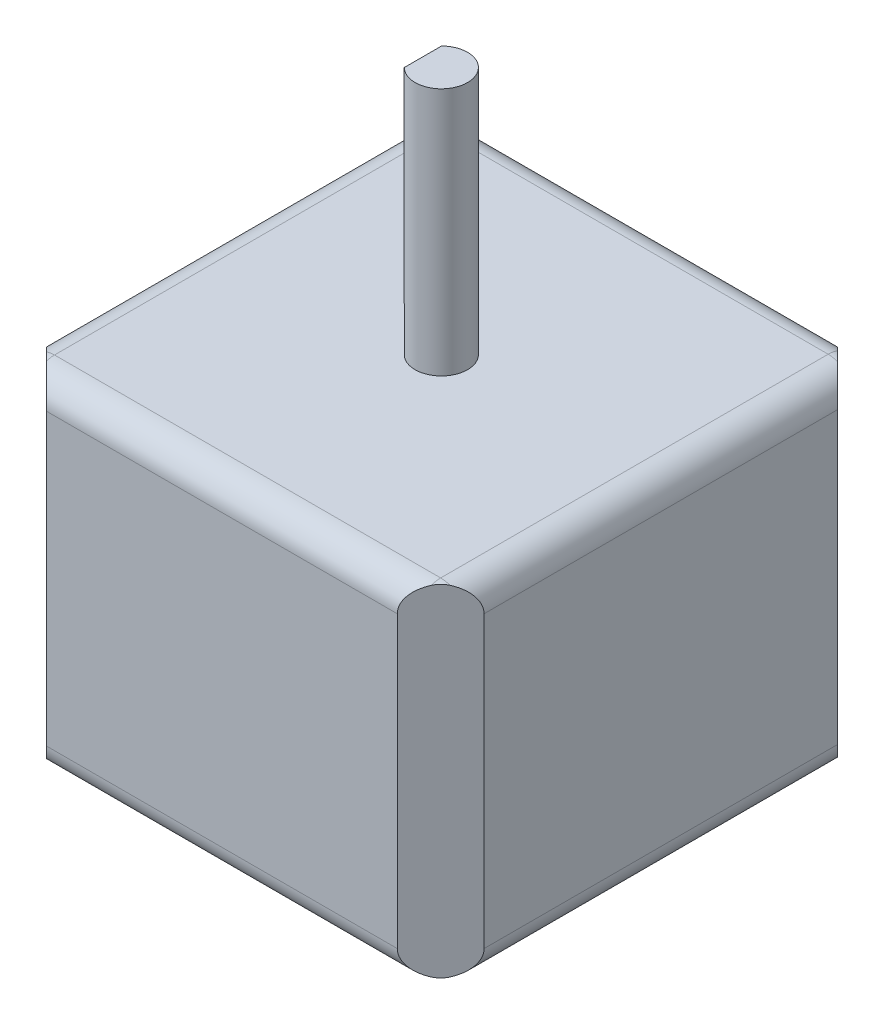
SolidWorks part; units mm, degrees
ref_plane "Front Plane" through (0, 0, 0) normal (0, 0, 1) x (1, 0, 0)
ref_plane "Top Plane" through (0, 0, 0) normal (0, 1, 0) x (1, 0, 0)
ref_plane "Right Plane" through (0, 0, 0) normal (1, 0, 0) x (0, 0, -1)
sketch "Sketch1" plane through (0, 0, 0) normal (0, 0, 1) x (1, 0, 0)
  line L0 (21.1455, 0) -> (-21.1455, 0) construction
  line L1 (21.1455, -16.51) -> (-21.1455, -16.51)
  line L2 (21.1455, -16.51) -> (21.1455, 16.51)
  line L3 (21.1455, 16.51) -> (-21.1455, 16.51)
  line L4 (-21.1455, -16.51) -> (-21.1455, 16.51)
  line L5 (21.1455, -16.51) -> (-21.1455, 16.51) construction
  line L6 (21.1455, 16.51) -> (-21.1455, -16.51) construction
  line L7 (0, 16.51) -> (0, -16.51) construction
  point P0 (0, 0)
  point P12 (0, 0)
  point P17 (0, 0)
  point P18 (0, 0)
  point P19 (52.1739, 16.51)
  point P20 (0, 0)
  dimension "D1" = 33.02
  dimension "D2" = 42.291
extrude "Boss-Extrude1" add sketch "Sketch1" along normal blind 42.418
fillet "Fillet1" radius 2.54 12 edges at (0, 16.51, 42.418) (21.1455, 0, 42.418) (0, -16.51, 42.418) (-21.1455, 0, 42.418) (-21.1455, 0, 0) (0, -16.51, 0) (-21.1455, -16.51, 21.209) (21.1455, -16.51, 21.209) (21.1455, 0, 0) (21.1455, 16.51, 21.209) (0, 16.51, 0) (-21.1455, 16.51, 21.209)
sketch "Sketch2" plane through (0, 16.51, 0) normal (0, 1, 0) x (1, 0, 0)
  line L2 (-18.6055, -2.54) -> (-18.6055, -39.878) construction
  circle A0 centre (0, -21.209) radius 2.5273
  point P7 (-18.6055, -21.209)
  dimension "D1" = 5.0546
extrude "Boss-Extrude2" add sketch "Sketch2" along normal blind 23.9649
sketch "Sketch4" plane through (0, 40.4749, 0) normal (0, 1, 0) x (1, 0, 0)
  line L0 (-1.778, -19.4129) -> (-1.778, -23.0051)
  line L1 (0, -18.6817) -> (0, -23.7363) construction
  circle A0 centre (0, -21.209) radius 2.5273
  circle A1 centre (0, -21.209) radius 2.5273 construction
  circle M4 centre (0, -21.209) radius 2.5273
  dimension "D1" = 1.778
extrude "Cut-Extrude2" cut sketch "Sketch4" against normal blind 18.288 contours L0 M4
sketch "Sketch5" plane through (0, -16.51, 0) normal (0, -1, 0) x (1, 0, 0)
  line L0 (-21.1455, 2.54) -> (-21.1455, 39.878) construction
  line L1 (21.2725, 0) -> (-21.1455, 0)
  line L2 (21.2725, 0) -> (21.2725, 42.418)
  line L3 (21.2725, 42.418) -> (-21.1455, 42.418)
  line L4 (-21.1455, 0) -> (-21.1455, 42.418)
  line L5 (21.2725, 0) -> (-21.1455, 42.418) construction
  line L6 (21.2725, 42.418) -> (-21.1455, 0) construction
  line L7 (18.6055, 0) -> (-18.6055, 0) construction
  line L8 (-18.6055, 42.418) -> (18.6055, 42.418) construction
  line L9 (-21.1455, 42.418) -> (-16.835, 42.418)
  line L10 (-21.1455, 42.418) -> (-21.1455, 38.1075)
  line L11 (-21.1455, 38.1075) -> (-16.835, 42.418)
  line L12 (21.2725, 42.418) -> (16.962, 42.418)
  line L13 (21.2725, 42.418) -> (21.2725, 38.1075)
  line L14 (21.2725, 38.1075) -> (16.962, 42.418)
  line L15 (-21.1455, 21.209) -> (21.2725, 21.209) construction
  line L16 (21.2725, 0) -> (21.2725, 4.3105)
  line L17 (21.2725, 4.3105) -> (16.962, 0)
  line L18 (21.2725, 0) -> (16.962, 0)
  line L19 (-21.1455, 0) -> (-21.1455, 4.3105)
  line L20 (-21.1455, 0) -> (-16.835, 0)
  line L21 (-21.1455, 4.3105) -> (-16.835, 0)
  point P0 (0.0635, 21.209)
  dimension "D1" = 6.096
  dimension "D2" = 6.096
extrude "Cut-Extrude3" cut sketch "Sketch5" against normal up to next contours L4 L11 L3 | L14 L2 L3 | L21 L4 L1 | L16 L17 L18
